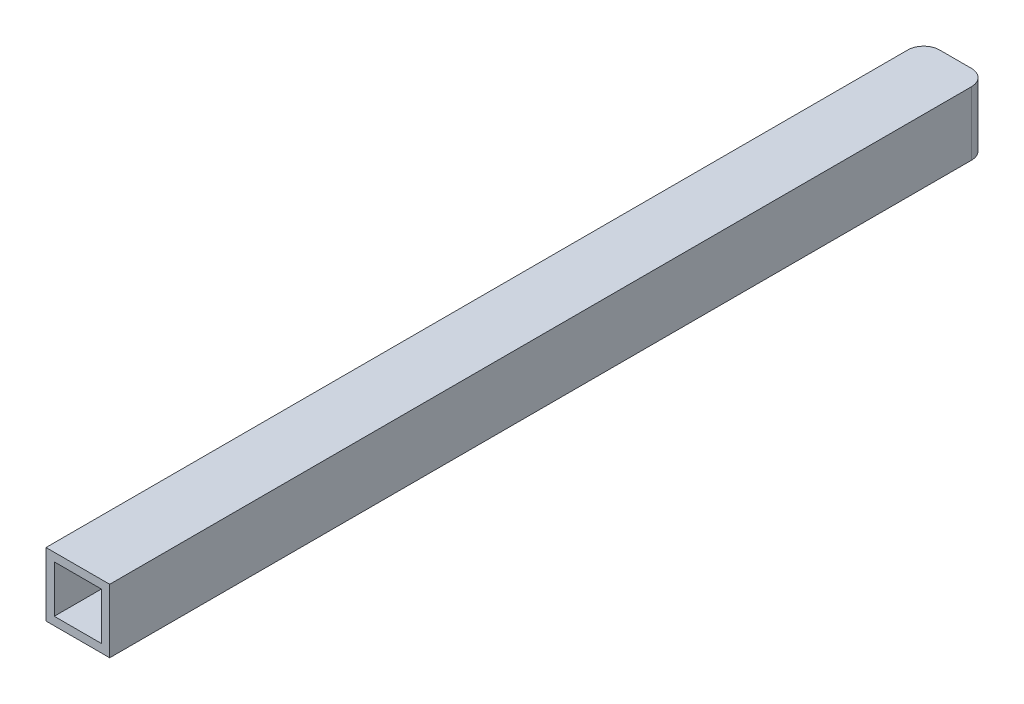
SolidWorks part; units mm, degrees
ref_plane "Front Plane" through (0, 0, 0) normal (0, 0, 1) x (1, 0, 0)
ref_plane "Top Plane" through (0, 0, 0) normal (0, 1, 0) x (1, 0, 0)
ref_plane "Right Plane" through (0, 0, 0) normal (1, 0, 0) x (0, 0, -1)
sketch "Sketch1" plane through (0, 0, 0) normal (0, 0, 1) x (1, 0, 0)
  line L1 (6.35, 6.35) -> (-6.35, 6.35)
  line L2 (6.35, 6.35) -> (6.35, -6.35)
  line L3 (6.35, -6.35) -> (-6.35, -6.35)
  line L4 (-6.35, 6.35) -> (-6.35, -6.35)
  line L5 (6.35, 6.35) -> (-6.35, -6.35) construction
  line L6 (6.35, -6.35) -> (-6.35, 6.35) construction
  line L7 (4.7, 4.7) -> (-4.7, 4.7)
  line L8 (4.7, 4.7) -> (4.7, -4.7)
  line L9 (4.7, -4.7) -> (-4.7, -4.7)
  line L10 (-4.7, 4.7) -> (-4.7, -4.7)
  line L11 (4.7, 4.7) -> (-4.7, -4.7) construction
  line L12 (4.7, -4.7) -> (-4.7, 4.7) construction
  point P0 (0, 0)
  point P5 (0, 0)
  dimension "D1" = 12.7
  dimension "D2" = 9.4
extrude "Boss-Extrude1" add sketch "Sketch1" along normal blind 175
sketch "Sketch2" plane through (0, 6.35, 0) normal (0, 1, 0) x (1, 0, 0)
  line L0 (-6.35, -175) -> (-6.35, 0) construction
  line L1 (6.35, 0) -> (-6.35, 0) construction
  line L2 (6.35, -175) -> (6.35, 0) construction
  line L3 (-4.7, 0) -> (4.7, 0) construction
  line L4 (-6.35, -3.175) -> (-6.35, 0)
  line L5 (-6.35, 0) -> (-3.175, 0)
  line L6 (3.175, 0) -> (6.35, 0)
  line L7 (6.35, 0) -> (6.35, -3.175)
  arc A0 (-6.35, -3.175) -> (-3.175, 0) centre (-3.175, -3.175) cw
  arc A1 (3.175, 0) -> (6.35, -3.175) centre (3.175, -3.175) cw
  dimension "D1" = 3.175
extrude "Cut-Extrude1" cut sketch "Sketch2" against normal through all
sketch "Sketch3" plane through (0, 6.35, 0) normal (0, 1, 0) x (1, 0, 0)
  line L0 (-3.175, 0) -> (-6.35, 0) construction
  line L1 (-6.35, 0) -> (-6.35, -3.175) construction
sketch "Sketch4" plane through (0, -6.35, 0) normal (0, -1, 0) x (1, 0, 0)
  line L0 (-3.175, 0) -> (3.175, 0) construction
  line L1 (-3.175, 0) -> (3.175, 0)
  arc A0 (3.175, 0) -> (6.35, 3.175) centre (3.175, 3.175) ccw construction
  arc A1 (-6.35, 3.175) -> (-3.175, 0) centre (-3.175, 3.175) ccw construction
  arc A2 (3.175, 0) -> (6.35, 3.175) centre (3.175, 3.175) ccw
  arc A3 (-6.35, 3.175) -> (-3.175, 0) centre (-3.175, 3.175) ccw
